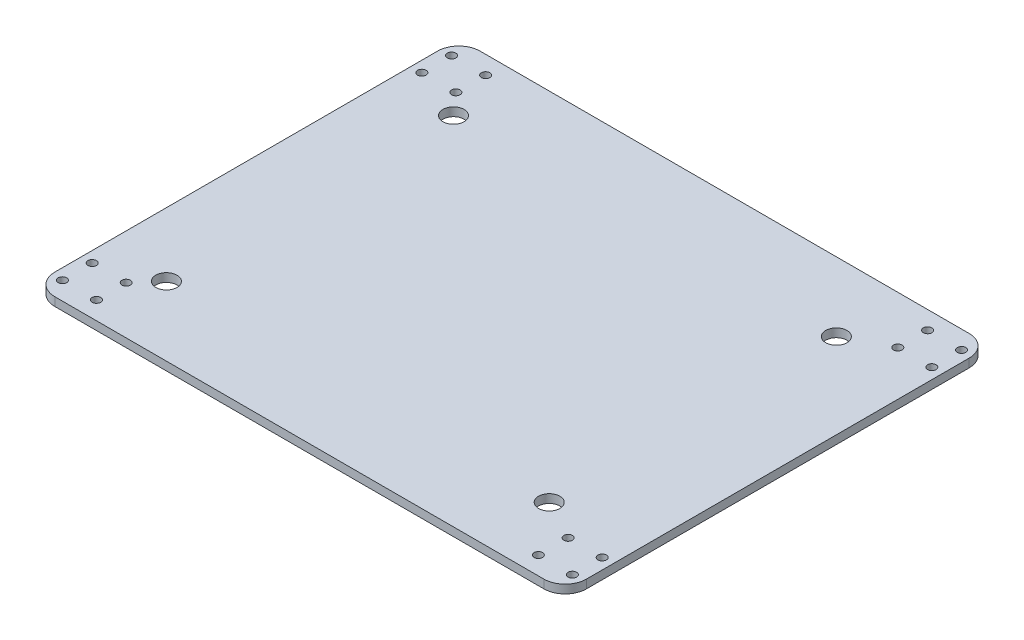
SolidWorks part; units mm, degrees
ref_plane "Front Plane" through (0, 0, 0) normal (0, 0, 1) x (1, 0, 0)
ref_plane "Top Plane" through (0, 0, 0) normal (0, 1, 0) x (1, 0, 0)
ref_plane "Right Plane" through (0, 0, 0) normal (1, 0, 0) x (0, 0, -1)
sketch "Sketch1" plane through (0, 0, 0) normal (0, 1, 0) x (1, 0, 0)
  line L1 (150, 5.3239) -> (400, 5.3239)
  line L2 (150, 5.3239) -> (150, 205.3239)
  line L3 (150, 205.3239) -> (400, 205.3239)
  line L4 (400, 5.3239) -> (400, 205.3239)
  dimension "D1" = 250
  dimension "D2" = 200
extrude "Boss-Extrude1" add sketch "Sketch1" along normal blind 4
sketch "Sketch4" plane through (0, 4, 0) normal (0, 1, 0) x (1, 0, 0)
  line L0 (360, 37.8239) -> (360, 172.8239)
  line L1 (180, 172.8239) -> (180, 37.8239)
  line L2 (180, 105.3239) -> (360, 105.3239) construction
  line L3 (270, 172.8239) -> (270, 37.8239) construction
  line L8 (120, 235.3239) -> (120, -24.6761)
  line L9 (120, -24.6761) -> (430, -24.6761)
  line L10 (430, -24.6761) -> (430, 235.3239)
  line L11 (430, 235.3239) -> (120, 235.3239)
  line L12 (120, 235.3239) -> (120, -24.6761)
  line L13 (120, -24.6761) -> (430, -24.6761)
  line L14 (430, -24.6761) -> (430, 235.3239)
  line L15 (430, 235.3239) -> (120, 235.3239)
  line L16 (180, 175.3239) -> (180, 35.3239)
  line L17 (180, 35.3239) -> (370, 35.3239)
  line L18 (370, 35.3239) -> (370, 175.3239)
  line L19 (370, 175.3239) -> (180, 175.3239)
  line L20 (180, 172.8239) -> (180, 37.8239)
  line L21 (180, 37.8239) -> (360, 37.8239)
  line L22 (360, 37.8239) -> (360, 172.8239)
  line L23 (360, 172.8239) -> (180, 172.8239)
  circle A0 centre (360, 37.8239) radius 5
  circle A1 centre (180, 37.8239) radius 5
  circle A2 centre (360, 172.8239) radius 5
  circle A3 centre (180, 172.8239) radius 5
  point P20 (-35.2731, 117.7357)
  dimension "D7" = 10
  dimension "D3" = 180
  dimension "D4" = 135
  dimension "D6" = 180
  dimension "D8" = 62.5
  dimension "D9" = 62.5
  dimension "D1" = 30
  dimension "D2" = 30
  dimension "D5" = 0
extrude "Cut-Extrude1" cut sketch "Sketch4" against normal through all contours A3 | A2 | A1 | A0
sketch "Sketch9" plane through (0, 0, 0) normal (0, -1, 0) x (1, 0, 0)
  line L0 (275, -5.3239) -> (275, -205.3239) construction
  line L1 (150, -5.3239) -> (400, -5.3239) construction
  line L2 (155.1, -205.3239) -> (155.1, -5.3239)
  line L3 (155.1, -205.3239) -> (155.1, -5.3239)
  line L4 (400, -205.3239) -> (150, -205.3239) construction
  line L5 (394.9, -5.3239) -> (394.9, -205.3239)
  line L6 (394.9, -5.3239) -> (394.9, -205.3239)
  line L7 (150, -105.3239) -> (400, -105.3239) construction
  line L8 (150, -205.3239) -> (150, -5.3239) construction
  line L9 (400, -5.3239) -> (400, -205.3239) construction
  line L11 (400, -196.8239) -> (150, -196.8239)
  line L12 (400, -196.8239) -> (150, -196.8239)
  line L14 (150, -13.8239) -> (400, -13.8239)
  line L15 (150, -13.8239) -> (400, -13.8239)
  circle A0 centre (155.1, -196.8239) radius 2
  circle A1 centre (155.1, -182.8239) radius 2
  circle A2 centre (171.1, -196.8239) radius 2
  circle A3 centre (171.1, -182.8239) radius 2
  circle A4 centre (155.1, -27.8239) radius 2
  circle A5 centre (155.1, -13.8239) radius 2
  circle A6 centre (171.1, -13.8239) radius 2
  circle A7 centre (171.1, -27.8239) radius 2
  circle A8 centre (394.9, -182.8239) radius 2
  circle A9 centre (394.9, -196.8239) radius 2
  circle A10 centre (378.9, -196.8239) radius 2
  circle A11 centre (378.9, -182.8239) radius 2
  circle A12 centre (394.9, -27.8239) radius 2
  circle A13 centre (378.9, -27.8239) radius 2
  circle A14 centre (378.9, -13.8239) radius 2
  circle A15 centre (394.9, -13.8239) radius 2
  dimension "D5" = 4
  dimension "D6" = 4
  dimension "D7" = 14
  dimension "D8" = 4
  dimension "D9" = 16
  dimension "D10" = 4
  dimension "D11" = 14
  dimension "D12" = 16
  dimension "D1" = 5.1
  dimension "D2" = 5.1
  dimension "D3" = 8.5
  dimension "D4" = 8.5
extrude "Cut-Extrude5" cut sketch "Sketch9" against normal through all contours A0 | A2 | A3 | A1 | A7 | A6 | A4 | A5 | A13 | A14 | A15 | A12 | A10 | A11 | A8 | A9
fillet "Fillet1" radius 10 4 edges at (150, 2, -205.3239) (150, 2, -5.3239) (400, 2, -5.3239) (400, 2, -205.3239)
